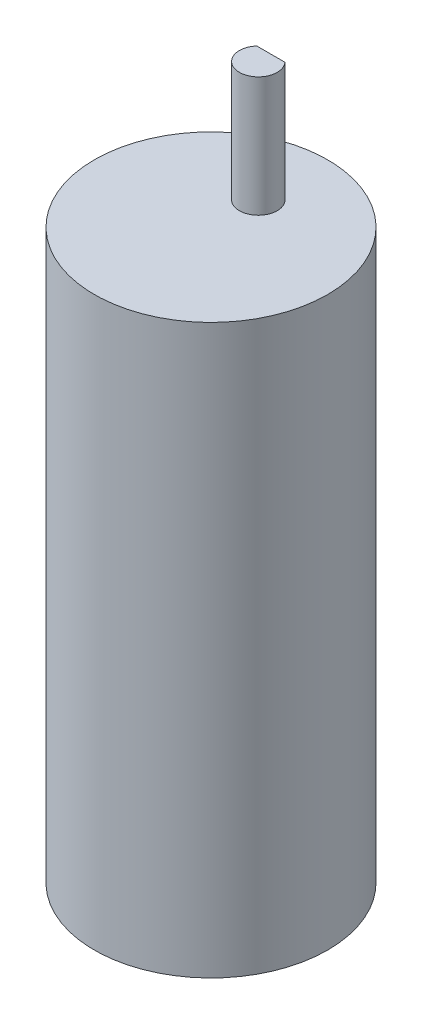
SolidWorks part; units mm, degrees
material "1.4541 (X6CrNiTi18-10)"
ref_plane "Plano frontal" through (0, 0, 0) normal (0, 0, 1) x (1, 0, 0)
ref_plane "Plano superior" through (0, 0, 0) normal (0, 1, 0) x (1, 0, 0)
ref_plane "Plano direito" through (0, 0, 0) normal (1, 0, 0) x (0, 0, -1)
sketch "Esboço1" plane through (0, 0, 0) normal (0, 0, 1) x (1, 0, 0)
  line L0 (0, 0) -> (18.5, 0)
  line L1 (18.5, 0) -> (18.5, -90)
  line L2 (18.5, -90) -> (0, -90)
  line L3 (0, -90) -> (0, 0) construction
  line L4 (0, 0) -> (0, -90)
  dimension "D1" = 37
  dimension "D2" = 90
revolve "Revolução1" add sketch "Esboço1" angle 360 about L3
sketch "Esboço2" plane through (0, 0, 0) normal (0, 1, 0) x (1, 0, 0)
  line L0 (0, 7.5) -> (0, 18.5) construction
  line L1 (-2.2361, 9.5) -> (2.2361, 9.5)
  arc A0 (-2.2361, 9.5) -> (2.2361, 9.5) centre (0, 7.5) ccw
  circle A1 centre (0, 0) radius 18.5 construction
  dimension "D1" = 6
  dimension "D2" = 2
extrude "Ressalto-extrusão1" add sketch "Esboço2" along normal blind 19
